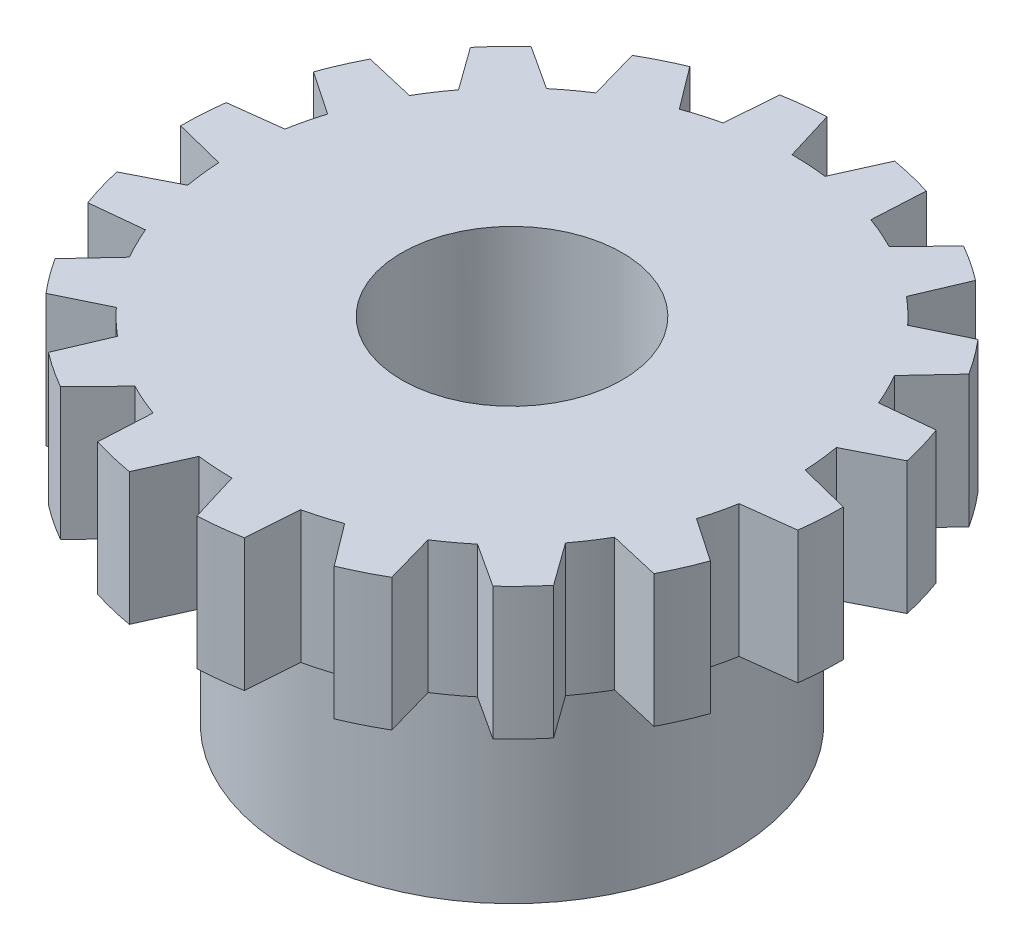
SolidWorks part; units mm, degrees
material "Cast Stainless Steel"
ref_plane "Front Plane" through (0, 0, 0) normal (0, 0, 1) x (1, 0, 0)
ref_plane "Top Plane" through (0, 0, 0) normal (0, 1, 0) x (1, 0, 0)
ref_plane "Right Plane" through (0, 0, 0) normal (1, 0, 0) x (0, 0, -1)
sketch "Sketch1" plane through (0, 0, 0) normal (0, 1, 0) x (1, 0, 0)
  circle A0 centre (0, 0) radius 7.5
  dimension "D1" = 15
extrude "Boss-Extrude1" add sketch "Sketch1" along normal blind 3
sketch "Sketch2" plane through (0, 0, 0) normal (0, -1, 0) x (-1, 0, 0)
  circle A0 centre (0, 0) radius 5
  dimension "D1" = 10
extrude "Boss-Extrude2" add sketch "Sketch2" along normal blind 5
sketch "Sketch3" plane through (0, 3, 0) normal (0, 1, 0) x (1, 0, 0)
  circle A0 centre (0, 0) radius 2.5
  dimension "D1" = 5
extrude "Cut-Extrude1" cut sketch "Sketch3" against normal up to next
sketch "Sketch4" plane through (0, 3, 0) normal (0, 1, 0) x (1, 0, 0)
  line L0 (-1.2891, -7.3884) -> (-0.8, -6.2994)
  line L1 (0.3481, -7.4919) -> (0, -6.35)
  line L2 (-2.2353, -7.1592) -> (-2.1718, -5.967)
  line L3 (-3.7384, -6.5019) -> (-2.9062, -5.6459)
  line L4 (-4.549, -5.9629) -> (-4.0817, -4.8644)
  line L5 (-5.7367, -4.8312) -> (-4.662, -4.3114)
  line L6 (-6.3141, -4.0474) -> (-5.4993, -3.175)
  line L7 (-7.0431, -2.5778) -> (-5.8554, -2.4569)
  line L8 (-7.3176, -1.6438) -> (-6.2535, -1.1027)
  line L9 (-7.5, -0.0134) -> (-6.3426, -0.3061)
  line L10 (-7.4385, 0.9581) -> (-6.2535, 1.1027)
  line L11 (-7.0523, 2.5525) -> (-6.0648, 1.8817)
  line L12 (-6.6622, 3.4445) -> (-5.4993, 3.175)
  line L13 (-5.7539, 4.8106) -> (-5.0555, 3.8425)
  line L14 (-5.0824, 5.5154) -> (-4.0817, 4.8644)
  line L15 (-3.7616, 6.4885) -> (-3.4364, 5.3398)
  line L16 (-2.8895, 6.921) -> (-2.1718, 5.967)
  line L17 (-1.3156, 7.3837) -> (-1.4028, 6.1931)
  line L18 (-0.3481, 7.4919) -> (0, 6.35)
  line L19 (1.2891, 7.3884) -> (0.8, 6.2994)
  line L20 (2.2353, 7.1592) -> (2.1718, 5.967)
  line L21 (3.7384, 6.5019) -> (2.9062, 5.6459)
  line L22 (4.549, 5.9629) -> (4.0817, 4.8644)
  line L23 (5.7367, 4.8312) -> (4.662, 4.3114)
  line L24 (6.3141, 4.0474) -> (5.4993, 3.175)
  line L25 (7.0431, 2.5778) -> (5.8554, 2.4569)
  line L26 (7.3176, 1.6438) -> (6.2535, 1.1027)
  line L27 (7.5, 0.0134) -> (6.3426, 0.3061)
  line L28 (7.4385, -0.9581) -> (6.2535, -1.1027)
  line L29 (7.0523, -2.5525) -> (6.0648, -1.8817)
  line L30 (6.6622, -3.4445) -> (5.4993, -3.175)
  line L31 (5.7539, -4.8106) -> (5.0555, -3.8425)
  line L32 (5.0824, -5.5154) -> (4.0817, -4.8644)
  line L33 (3.7616, -6.4885) -> (3.4364, -5.3398)
  line L34 (2.8895, -6.921) -> (2.1718, -5.967)
  line L35 (1.3156, -7.3837) -> (1.4028, -6.1931)
  circle A0 centre (0, 0) radius 7.5 construction
  circle A1 centre (0, 0) radius 6.35 construction
  arc A2 (-0.8, -6.2994) -> (0, -6.35) centre (0, 0) ccw
  arc A3 (-1.2891, -7.3884) -> (0.3481, -7.4919) centre (0, 0) ccw
  arc A4 (-2.9062, -5.6459) -> (-2.1718, -5.967) centre (0, 0) ccw
  arc A5 (-3.7384, -6.5019) -> (-2.2353, -7.1592) centre (0, 0) ccw
  arc A6 (-4.662, -4.3114) -> (-4.0817, -4.8644) centre (0, 0) ccw
  arc A7 (-5.7367, -4.8312) -> (-4.549, -5.9629) centre (0, 0) ccw
  arc A8 (-5.8554, -2.4569) -> (-5.4993, -3.175) centre (0, 0) ccw
  arc A9 (-7.0431, -2.5778) -> (-6.3141, -4.0474) centre (0, 0) ccw
  arc A10 (-6.3426, -0.3061) -> (-6.2535, -1.1027) centre (0, 0) ccw
  arc A11 (-7.5, -0.0134) -> (-7.3176, -1.6438) centre (0, 0) ccw
  arc A12 (-6.0648, 1.8817) -> (-6.2535, 1.1027) centre (0, 0) ccw
  arc A13 (-7.0523, 2.5525) -> (-7.4385, 0.9581) centre (0, 0) ccw
  arc A14 (-5.0555, 3.8425) -> (-5.4993, 3.175) centre (0, 0) ccw
  arc A15 (-5.7539, 4.8106) -> (-6.6622, 3.4445) centre (0, 0) ccw
  arc A16 (-3.4364, 5.3398) -> (-4.0817, 4.8644) centre (0, 0) ccw
  arc A17 (-3.7616, 6.4885) -> (-5.0824, 5.5154) centre (0, 0) ccw
  arc A18 (-1.4028, 6.1931) -> (-2.1718, 5.967) centre (0, 0) ccw
  arc A19 (-1.3156, 7.3837) -> (-2.8895, 6.921) centre (0, 0) ccw
  arc A20 (0.8, 6.2994) -> (0, 6.35) centre (0, 0) ccw
  arc A21 (1.2891, 7.3884) -> (-0.3481, 7.4919) centre (0, 0) ccw
  arc A22 (2.9062, 5.6459) -> (2.1718, 5.967) centre (0, 0) ccw
  arc A23 (3.7384, 6.5019) -> (2.2353, 7.1592) centre (0, 0) ccw
  arc A24 (4.662, 4.3114) -> (4.0817, 4.8644) centre (0, 0) ccw
  arc A25 (5.7367, 4.8312) -> (4.549, 5.9629) centre (0, 0) ccw
  arc A26 (5.8554, 2.4569) -> (5.4993, 3.175) centre (0, 0) ccw
  arc A27 (7.0431, 2.5778) -> (6.3141, 4.0474) centre (0, 0) ccw
  arc A28 (6.3426, 0.3061) -> (6.2535, 1.1027) centre (0, 0) ccw
  arc A29 (7.5, 0.0134) -> (7.3176, 1.6438) centre (0, 0) ccw
  arc A30 (6.0648, -1.8817) -> (6.2535, -1.1027) centre (0, 0) ccw
  arc A31 (7.0523, -2.5525) -> (7.4385, -0.9581) centre (0, 0) ccw
  arc A32 (5.0555, -3.8425) -> (5.4993, -3.175) centre (0, 0) ccw
  arc A33 (5.7539, -4.8106) -> (6.6622, -3.4445) centre (0, 0) ccw
  arc A34 (3.4364, -5.3398) -> (4.0817, -4.8644) centre (0, 0) ccw
  arc A35 (3.7616, -6.4885) -> (5.0824, -5.5154) centre (0, 0) ccw
  arc A36 (1.4028, -6.1931) -> (2.1718, -5.967) centre (0, 0) ccw
  arc A37 (1.3156, -7.3837) -> (2.8895, -6.921) centre (0, 0) ccw
  point P80 (0, 0)
  dimension "D1" = 12.7
  dimension "D2" = 1.6373
  dimension "D3" = 1.1938
  dimension "D4" = 18
extrude "Cut-Extrude2" cut sketch "Sketch4" against normal up to next
